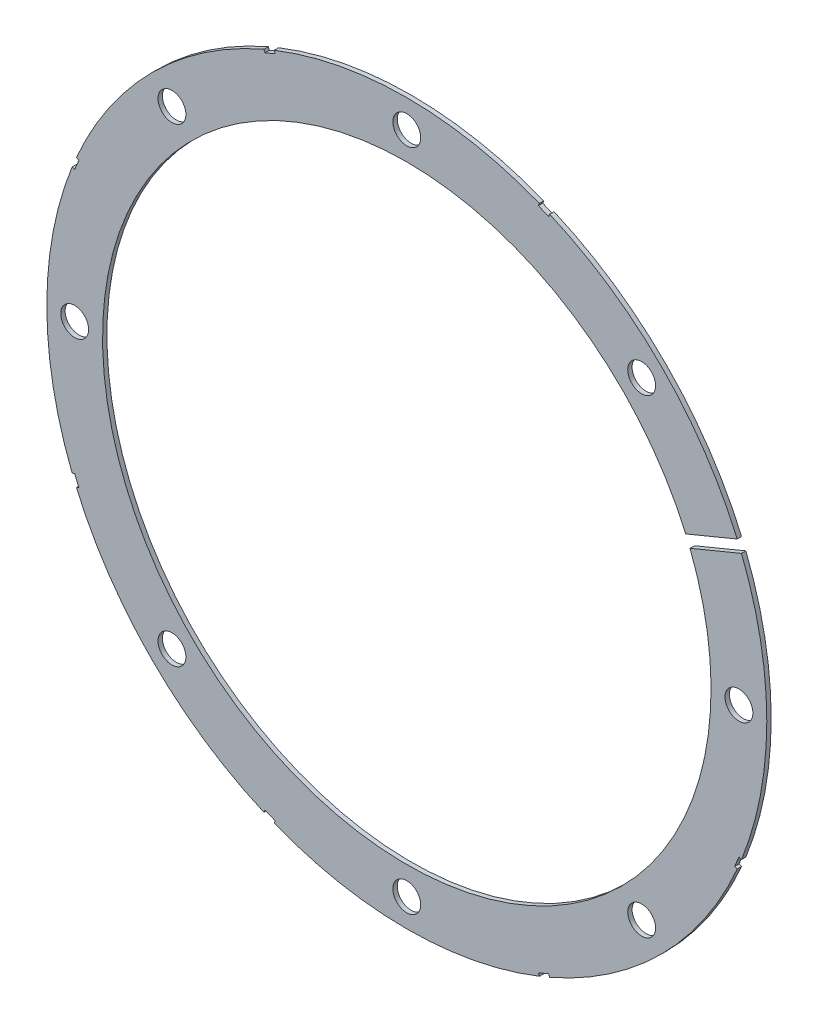
SolidWorks part; units mm, degrees
material "Copper"
ref_plane "Front Plane" through (0, 0, 0) normal (0, 0, 1) x (1, 0, 0)
ref_plane "Top Plane" through (0, 0, 0) normal (0, 1, 0) x (1, 0, 0)
ref_plane "Right Plane" through (0, 0, 0) normal (1, 0, 0) x (0, 0, -1)
sketch "Sketch4" plane through (0, 0, 0) normal (0, 0, 1) x (1, 0, 0)
  circle A0 centre (0, 0) radius 82.042
  dimension "D1" = 164.084
extrude "Boss-Extrude2" add sketch "Sketch4" along normal blind 1
sketch "Sketch5" plane through (0, 0, 1) normal (0, 0, 1) x (1, 0, 0)
  circle A0 centre (0, 0) radius 69.342
  circle A1 centre (0, 0) radius 82.042 construction
  dimension "D2" = 12.7
extrude "Cut-Extrude5" cut sketch "Sketch5" against normal through all
sketch "Sketch6" plane through (0, 0, 1) normal (0, 0, 1) x (1, 0, 0)
  circle A0 centre (75.692, 0) radius 3.175
  circle A4 centre (0, 0) radius 82.042 construction
  dimension "D2" = 6.35
  dimension "D1" = 6.35
extrude "Cut-Extrude6" cut sketch "Sketch6" against normal through all
pattern_circular "CirPattern1" count 8 over 360 about axis through (0, 0, 0) along (0, 0, 1) of "Cut-Extrude6"
sketch "Sketch8" plane through (0, 0, 1) normal (0, 0, 1) x (1, 0, 0)
  line L0 (78.8309, 34.0275) -> (60.0577, 26.2513)
  line L1 (78.8309, 34.0275) -> (79.8029, 31.6808)
  line L2 (60.0577, 26.2513) -> (61.0297, 23.9047)
  line L3 (79.8029, 31.6808) -> (61.0297, 23.9047)
  line L4 (78.8309, 34.0275) -> (61.0297, 23.9047) construction
  line L5 (60.0577, 26.2513) -> (79.8029, 31.6808) construction
  line L6 (0, 0) -> (82.042, 0) construction
  line L7 (32.8124, 75.8976) -> (30.4658, 76.8696)
  line L8 (32.8124, 75.8976) -> (32.3264, 74.7243)
  line L9 (30.4658, 76.8696) -> (29.9798, 75.6963)
  line L10 (32.3264, 74.7243) -> (29.9798, 75.6963)
  line L11 (30.4658, 76.8696) -> (32.3264, 74.7243) construction
  line L12 (32.8124, 75.8976) -> (29.9798, 75.6963) construction
  line L13 (-30.4658, 76.8696) -> (-32.8124, 75.8976)
  line L14 (-30.4658, 76.8696) -> (-29.9798, 75.6963)
  line L15 (-29.9798, 75.6963) -> (-32.3264, 74.7243)
  line L16 (-32.8124, 75.8976) -> (-32.3264, 74.7243)
  line L17 (-30.4658, 76.8696) -> (-32.3264, 74.7243) construction
  line L18 (-32.8124, 75.8976) -> (-29.9798, 75.6963) construction
  line L19 (-75.8976, 32.8124) -> (-76.8696, 30.4658)
  line L20 (-75.8976, 32.8124) -> (-74.7243, 32.3264)
  line L21 (-74.7243, 32.3264) -> (-75.6963, 29.9798)
  line L22 (-76.8696, 30.4658) -> (-75.6963, 29.9798)
  line L23 (-75.8976, 32.8124) -> (-75.6963, 29.9798) construction
  line L24 (-76.8696, 30.4658) -> (-74.7243, 32.3264) construction
  line L25 (-76.8696, -30.4658) -> (-75.8976, -32.8124)
  line L26 (-76.8696, -30.4658) -> (-75.6963, -29.9798)
  line L27 (-75.6963, -29.9798) -> (-74.7243, -32.3264)
  line L28 (-75.8976, -32.8124) -> (-74.7243, -32.3264)
  line L29 (-76.8696, -30.4658) -> (-74.7243, -32.3264) construction
  line L30 (-75.8976, -32.8124) -> (-75.6963, -29.9798) construction
  line L31 (-32.8124, -75.8976) -> (-30.4658, -76.8696)
  line L32 (-32.8124, -75.8976) -> (-32.3264, -74.7243)
  line L33 (-32.3264, -74.7243) -> (-29.9798, -75.6963)
  line L34 (-30.4658, -76.8696) -> (-29.9798, -75.6963)
  line L35 (-32.8124, -75.8976) -> (-29.9798, -75.6963) construction
  line L36 (-30.4658, -76.8696) -> (-32.3264, -74.7243) construction
  line L37 (30.4658, -76.8696) -> (32.8124, -75.8976)
  line L38 (30.4658, -76.8696) -> (29.9798, -75.6963)
  line L39 (29.9798, -75.6963) -> (32.3264, -74.7243)
  line L40 (32.8124, -75.8976) -> (32.3264, -74.7243)
  line L41 (30.4658, -76.8696) -> (32.3264, -74.7243) construction
  line L42 (32.8124, -75.8976) -> (29.9798, -75.6963) construction
  line L43 (75.8976, -32.8124) -> (76.8696, -30.4658)
  line L44 (75.8976, -32.8124) -> (74.7243, -32.3264)
  line L45 (74.7243, -32.3264) -> (75.6963, -29.9798)
  line L46 (76.8696, -30.4658) -> (75.6963, -29.9798)
  line L47 (75.8976, -32.8124) -> (75.6963, -29.9798) construction
  line L48 (76.8696, -30.4658) -> (74.7243, -32.3264) construction
  circle A0 centre (0, 0) radius 82.042 construction
  point P1 (69.9303, 28.9661)
  point P3 (31.3961, 75.7969)
  point P11 (-31.3961, 75.7969)
  point P20 (-75.7969, 31.3961)
  point P25 (-75.7969, -31.3961)
  point P26 (0, 0)
  point P31 (-31.3961, -75.7969)
  point P36 (31.3961, -75.7969)
  point P41 (75.7969, -31.3961)
  point P46 (0, 0)
  dimension "D1" = 20.32
  dimension "D2" = 6.35
  dimension "D3" = 2.54
  dimension "D4" = 22.5
  dimension "D5" = 1.27
  dimension "D6" = 2.54
  dimension "D7" = 1.27
  dimension "D8" = 1.27
  dimension "D9" = 0.635
  dimension "D10" = 67.5
  dimension "D12" = 0.635
  dimension "D13" = 0.635
  dimension "D14" = 22.5
  dimension "D11" = 7
extrude "Cut-Extrude11" cut sketch "Sketch8" against normal through all
